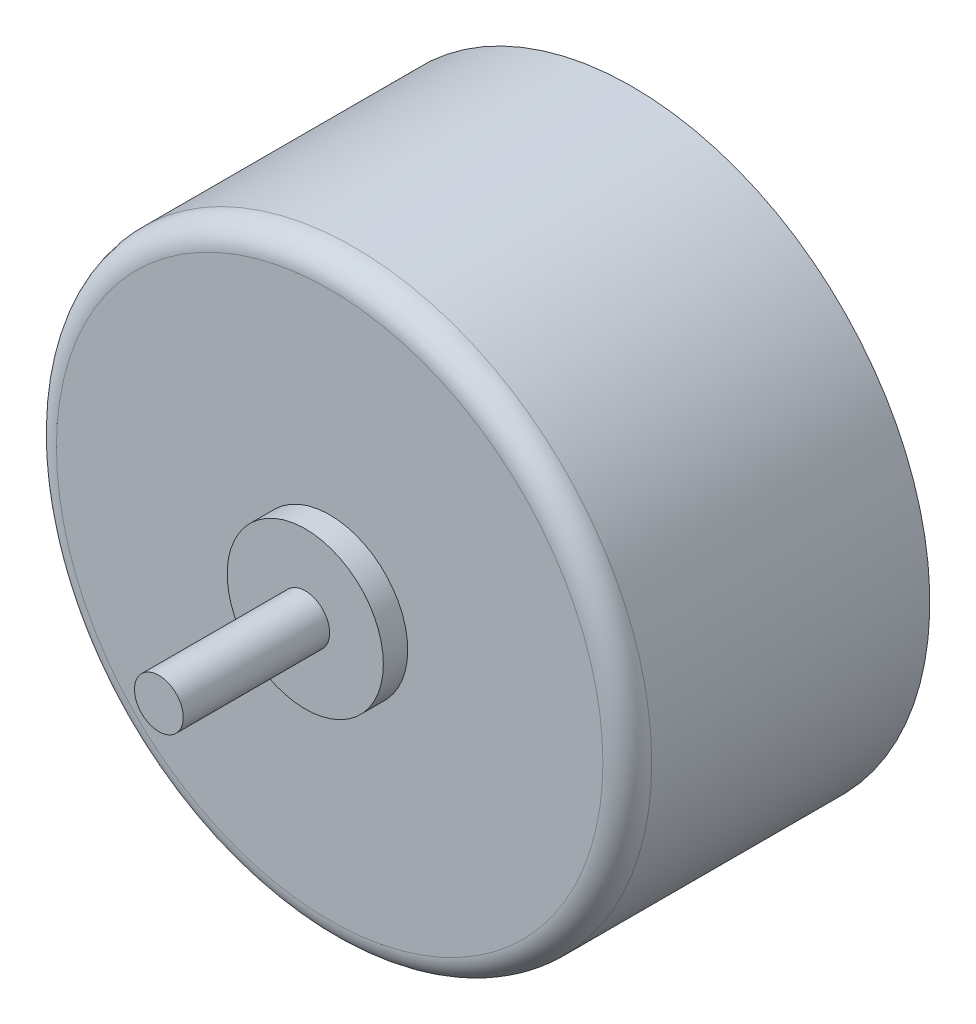
SolidWorks part; units mm, degrees
ref_plane "Front Plane" through (0, 0, 0) normal (0, 0, 1) x (1, 0, 0)
ref_plane "Top Plane" through (0, 0, 0) normal (0, 1, 0) x (1, 0, 0)
ref_plane "Right Plane" through (0, 0, 0) normal (1, 0, 0) x (0, 0, -1)
sketch "Sketch1" plane through (0, 0, 0) normal (0, 0, 1) x (1, 0, 0)
  circle A0 centre (0, 0) radius 12.2
  dimension "D1" = 24.4
extrude "Boss-Extrude1" add sketch "Sketch1" along normal blind 12.4
sketch "Sketch2" plane through (0, 0, 12.4) normal (0, 0, 1) x (1, 0, 0)
  circle A0 centre (0, 0) radius 1
  dimension "D1" = 2
extrude "Boss-Extrude2" add sketch "Sketch2" along normal blind 7
sketch "Sketch3" plane through (0, 0, 12.4) normal (0, 0, 1) x (1, 0, 0)
  circle A0 centre (0, 0) radius 3.2
  dimension "D1" = 6.4
extrude "Boss-Extrude3" add sketch "Sketch3" along normal blind 1
sketch "Sketch4" plane through (0, 0, 0) normal (1, 0, 0) x (0, 0, -1)
  line L0 (0, -12.2) -> (0, 12.2) construction
  line L1 (-4, 2) -> (0, 2)
  line L2 (-4, 2) -> (-4, -2)
  line L3 (-4, -2) -> (0, -2)
  line L4 (0, 2) -> (0, -2)
  circle A0 centre (-3, 1) radius 0.75
  circle A1 centre (-3, -1) radius 0.75
  point P6 (-4, 0)
  dimension "D3" = 1.5
  dimension "D4" = 1.5
  dimension "D1" = 4
  dimension "D2" = 4
  dimension "D5" = 1
  dimension "D6" = 1
  dimension "D7" = 1
  dimension "D8" = 1
extrude "Boss-Extrude4" add sketch "Sketch4" against normal blind 12.5
fillet "Fillet1" radius 1 1 edges at (12.2, 0, 12.4)
